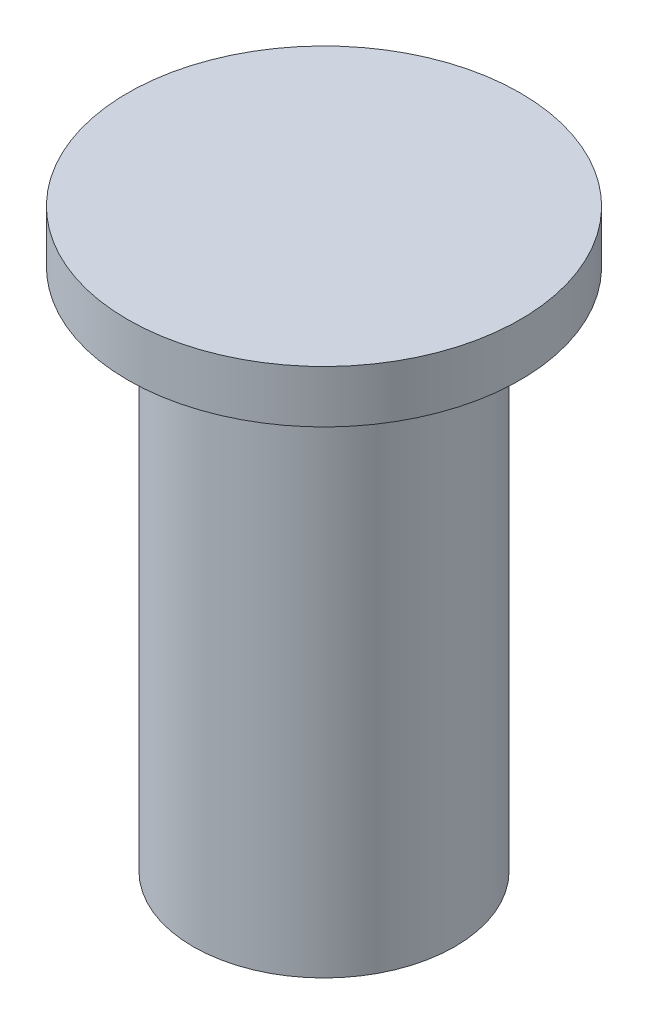
SolidWorks part; units mm, degrees
ref_plane "Front Plane" through (0, 0, 0) normal (0, 0, 1) x (1, 0, 0)
ref_plane "Top Plane" through (0, 0, 0) normal (0, 1, 0) x (1, 0, 0)
ref_plane "Right Plane" through (0, 0, 0) normal (1, 0, 0) x (0, 0, -1)
sketch "Sketch1" plane through (0, 0, 0) normal (0, 1, 0) x (1, 0, 0)
  circle A0 centre (0, 0) radius 6.35
  dimension "D1" = 12.7
extrude "Boss-Extrude1" add sketch "Sketch1" along normal blind 25.4
sketch "Sketch2" plane through (0, 25.4, 0) normal (0, 1, 0) x (1, 0, 0)
  circle A0 centre (0, 0) radius 9.525
  dimension "D1" = 19.05
extrude "Boss-Extrude2" add sketch "Sketch2" along normal blind 2.54 contours A0
